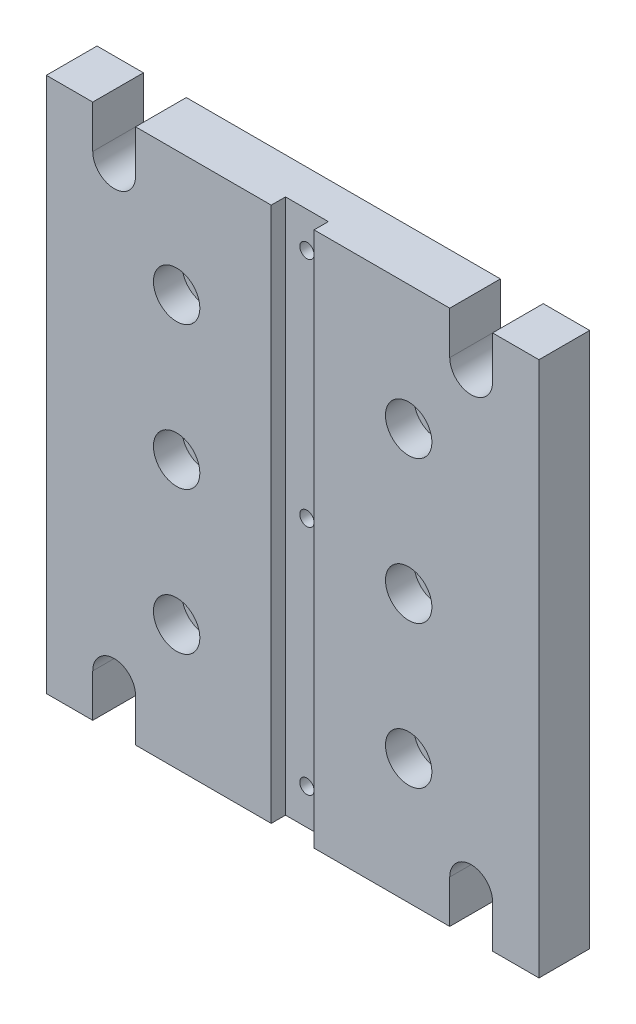
SolidWorks part; units mm, degrees
ref_plane "Alzado" through (0, 0, 0) normal (0, 0, 1) x (1, 0, 0)
ref_plane "Planta" through (0, 0, 0) normal (0, 1, 0) x (1, 0, 0)
ref_plane "Vista lateral" through (0, 0, 0) normal (1, 0, 0) x (0, 0, -1)
sketch "Croquis1" plane through (0, 0, 0) normal (0, 0, 1) x (1, 0, 0)
  line L0 (0, 75) -> (0, -75) construction
  line L1 (69, -75) -> (56, -75)
  line L2 (69, -75) -> (69, 75)
  line L3 (69, 75) -> (56, 75)
  line L4 (-69, -75) -> (-69, 75)
  line L5 (69, -75) -> (-69, 75) construction
  line L6 (69, 75) -> (-69, -75) construction
  line L7 (-69, 0) -> (69, 0) construction
  line L8 (-50, 75) -> (-50, 63) construction
  line L9 (50, 75) -> (50, 63) construction
  line L10 (50, -75) -> (50, -63) construction
  line L11 (-50, -75) -> (-50, -63) construction
  line L12 (-56, 63) -> (-56, 75)
  line L13 (-44, 63) -> (-44, 75)
  line L14 (44, 63) -> (44, 75)
  line L15 (56, 63) -> (56, 75)
  line L16 (44, -63) -> (44, -75)
  line L17 (56, -63) -> (56, -75)
  line L18 (-56, -63) -> (-56, -75)
  line L19 (-44, -63) -> (-44, -75)
  line L20 (-56, -75) -> (-69, -75)
  line L21 (44, -75) -> (-44, -75)
  line L22 (44, 75) -> (-44, 75)
  line L23 (-56, 75) -> (-69, 75)
  arc A0 (-56, 63) -> (-44, 63) centre (-50, 63) ccw
  arc A1 (44, 63) -> (56, 63) centre (50, 63) ccw
  arc A2 (56, -63) -> (44, -63) centre (50, -63) ccw
  arc A3 (-44, -63) -> (-56, -63) centre (-50, -63) ccw
  circle A4 centre (-32.5, 40) radius 4.25
  circle A5 centre (-32.5, 0) radius 4.25
  circle A6 centre (-32.5, -40) radius 4.25
  circle A7 centre (32.5, 40) radius 4.25
  circle A8 centre (32.5, 0) radius 4.25
  circle A9 centre (32.5, -40) radius 4.25
  circle A10 centre (0, 65) radius 2
  circle A11 centre (0, 0) radius 2
  circle A12 centre (0, -65) radius 2
  point P0 (0, 0)
  dimension "D5" = 12
  dimension "D10" = 8.5
  dimension "D18" = 4
  dimension "D1" = 138
  dimension "D2" = 150
  dimension "D3" = 50
  dimension "D4" = 50
  dimension "D6" = 12
  dimension "D7" = 12
  dimension "D8" = 12
  dimension "D9" = 12
  dimension "D11" = 23
  dimension "D12" = 40
  dimension "D13" = 40
  dimension "D14" = 23
  dimension "D15" = 36.5
  dimension "D16" = 65
  dimension "D17" = 36.5
  dimension "D19" = 65
  dimension "D20" = 65
  dimension "D21" = 10
extrude "Saliente-Extruir1" add sketch "Croquis1" along normal blind 14.2
sketch "Croquis2" plane through (0, 0, 14.2) normal (0, 0, 1) x (1, 0, 0)
  line L0 (0, 80.3173) -> (0, -81.994) construction
  line L1 (-6, 80.3173) -> (6, 80.3173)
  line L2 (-6, 80.3173) -> (-6, -81.994)
  line L3 (-6, -81.994) -> (6, -81.994)
  line L4 (6, 80.3173) -> (6, -81.994)
  dimension "D1" = 12
extrude "Cortar-Extruir1" cut sketch "Croquis2" against normal blind 4
sketch "Croquis3" plane through (0, 0, 14.2) normal (0, 0, 1) x (1, 0, 0)
  circle A0 centre (-32.5, 40) radius 6.5
  circle A1 centre (-32.5, 0) radius 6.5
  circle A2 centre (-32.5, -40) radius 6.5
  circle A3 centre (32.5, 40) radius 6.5
  circle A4 centre (32.5, 0) radius 6.5
  circle A5 centre (32.5, -40) radius 6.5
  dimension "D1" = 13
extrude "Cortar-Extruir2" cut sketch "Croquis3" against normal blind 8
